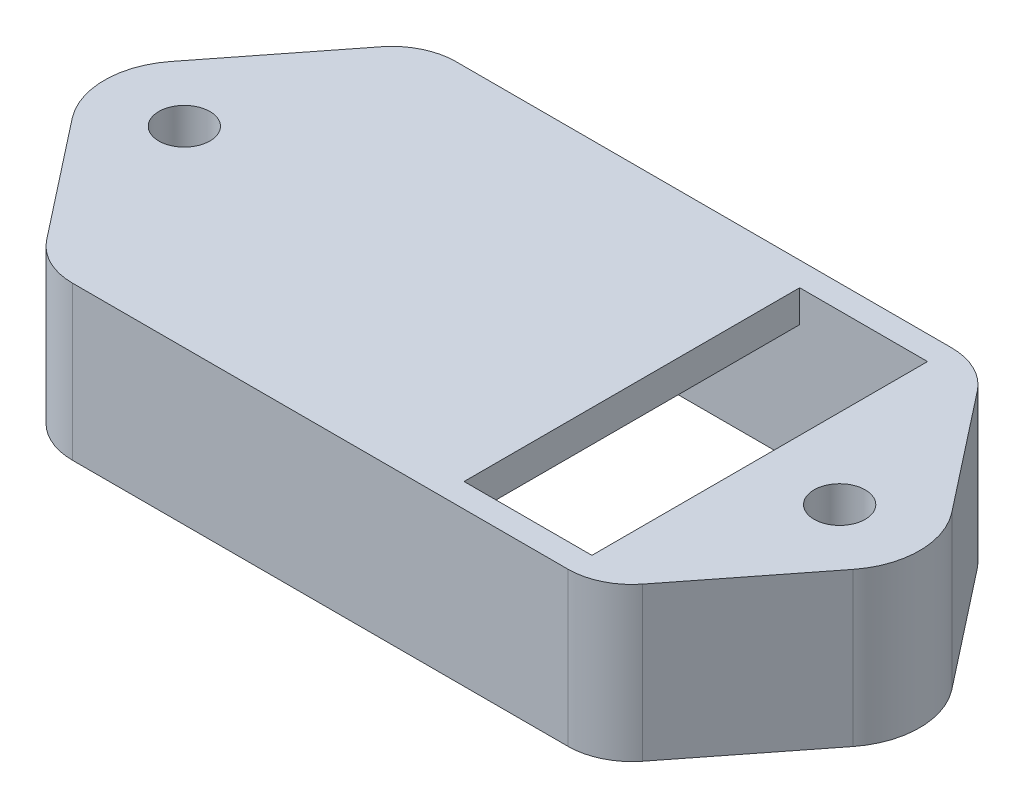
SolidWorks part; units mm, degrees
ref_plane "Front Plane" through (0, 0, 0) normal (0, 0, 1) x (1, 0, 0)
ref_plane "Top Plane" through (0, 0, 0) normal (0, 1, 0) x (1, 0, 0)
ref_plane "Right Plane" through (0, 0, 0) normal (1, 0, 0) x (0, 0, -1)
sketch "Sketch1" plane through (0, 0, 0) normal (0, 1, 0) x (1, 0, 0)
  line L0 (-7.75, 6) -> (7.75, 6)
  line L1 (-7.75, -5.25) -> (7.75, -5.25)
  line L2 (-7.75, -5.25) -> (-7.75, 5.25)
  line L3 (-7.75, 5.25) -> (7.75, 5.25)
  line L4 (7.75, -5.25) -> (7.75, 5.25)
  line L5 (9.3241, 5.2338) -> (12.2176, 1.5423)
  line L6 (0, 0) -> (0, 5.25) construction
  line L7 (-9.3241, 5.2338) -> (-12.2176, 1.5423)
  line L8 (0, 0) -> (7.75, 0) construction
  line L9 (-9.3241, -5.2338) -> (-12.2176, -1.5423)
  line L10 (9.3241, -5.2338) -> (12.2176, -1.5423)
  line L11 (-7.75, -6) -> (7.75, -6)
  arc A0 (7.75, 6) -> (9.3241, 5.2338) centre (7.75, 4) cw
  arc A1 (12.2176, 1.5423) -> (12.2176, -1.5423) centre (10.25, 0) cw
  circle A2 centre (10.25, 0) radius 0.8
  circle A3 centre (-10.25, 0) radius 0.8
  arc A4 (-12.2176, 1.5423) -> (-12.2176, -1.5423) centre (-10.25, 0) ccw
  arc A5 (-7.75, 6) -> (-9.3241, 5.2338) centre (-7.75, 4) ccw
  arc A6 (-7.75, -6) -> (-9.3241, -5.2338) centre (-7.75, -4) cw
  arc A7 (7.75, -6) -> (9.3241, -5.2338) centre (7.75, -4) ccw
  point P4 (0, 5.25)
  point P6 (7.75, 0)
  dimension "D4" = 1.6
  dimension "D5" = 2.5
  dimension "D6" = 2
  dimension "D1" = 15.5
  dimension "D2" = 10.5
  dimension "D3" = 0.75
  dimension "D7" = 2.5
extrude "Boss-Extrude1" add sketch "Sketch1" along normal blind 3.8
sketch "Sketch2" plane through (0, 3.8, 0) normal (0, 1, 0) x (1, 0, 0)
  line L0 (-7.75, -5.25) -> (7.75, -5.25) construction
  line L1 (3.75, -5.25) -> (7.75, -5.25)
  line L2 (3.75, -5.25) -> (3.75, 5.25)
  line L3 (3.75, 5.25) -> (7.75, 5.25)
  line L4 (7.75, -5.25) -> (7.75, 5.25)
  line L13 (-9.3241, 5.2338) -> (-12.2176, 1.5423)
  line L14 (-12.2176, -1.5423) -> (-9.3241, -5.2338)
  line L15 (-7.75, -6) -> (7.75, -6)
  line L16 (9.3241, -5.2338) -> (12.2176, -1.5423)
  line L17 (12.2176, 1.5423) -> (9.3241, 5.2338)
  line L18 (7.75, 6) -> (-7.75, 6)
  line L19 (-9.3241, 5.2338) -> (-12.2176, 1.5423)
  line L20 (-12.2176, -1.5423) -> (-9.3241, -5.2338)
  line L21 (-7.75, -6) -> (7.75, -6)
  line L22 (9.3241, -5.2338) -> (12.2176, -1.5423)
  line L23 (12.2176, 1.5423) -> (9.3241, 5.2338)
  line L24 (7.75, 6) -> (-7.75, 6)
  circle A0 centre (10.25, 0) radius 0.8 construction
  circle A1 centre (-10.25, 0) radius 0.8 construction
  circle A2 centre (10.25, 0) radius 0.8
  circle A3 centre (-10.25, 0) radius 0.8
  arc A6 (-7.75, 6) -> (-9.3241, 5.2338) centre (-7.75, 4) ccw
  arc A7 (-12.2176, 1.5423) -> (-12.2176, -1.5423) centre (-10.25, 0) ccw
  arc A8 (-9.3241, -5.2338) -> (-7.75, -6) centre (-7.75, -4) ccw
  arc A9 (7.75, -6) -> (9.3241, -5.2338) centre (7.75, -4) ccw
  arc A10 (12.2176, -1.5423) -> (12.2176, 1.5423) centre (10.25, 0) ccw
  arc A11 (9.3241, 5.2338) -> (7.75, 6) centre (7.75, 4) ccw
  arc A12 (-7.75, 6) -> (-9.3241, 5.2338) centre (-7.75, 4) ccw
  arc A13 (-12.2176, 1.5423) -> (-12.2176, -1.5423) centre (-10.25, 0) ccw
  arc A14 (-9.3241, -5.2338) -> (-7.75, -6) centre (-7.75, -4) ccw
  arc A15 (7.75, -6) -> (9.3241, -5.2338) centre (7.75, -4) ccw
  arc A16 (12.2176, -1.5423) -> (12.2176, 1.5423) centre (10.25, 0) ccw
  arc A17 (9.3241, 5.2338) -> (7.75, 6) centre (7.75, 4) ccw
  dimension "D1" = 4
  dimension "D2" = 0
extrude "Boss-Extrude2" add sketch "Sketch2" along normal blind 1
